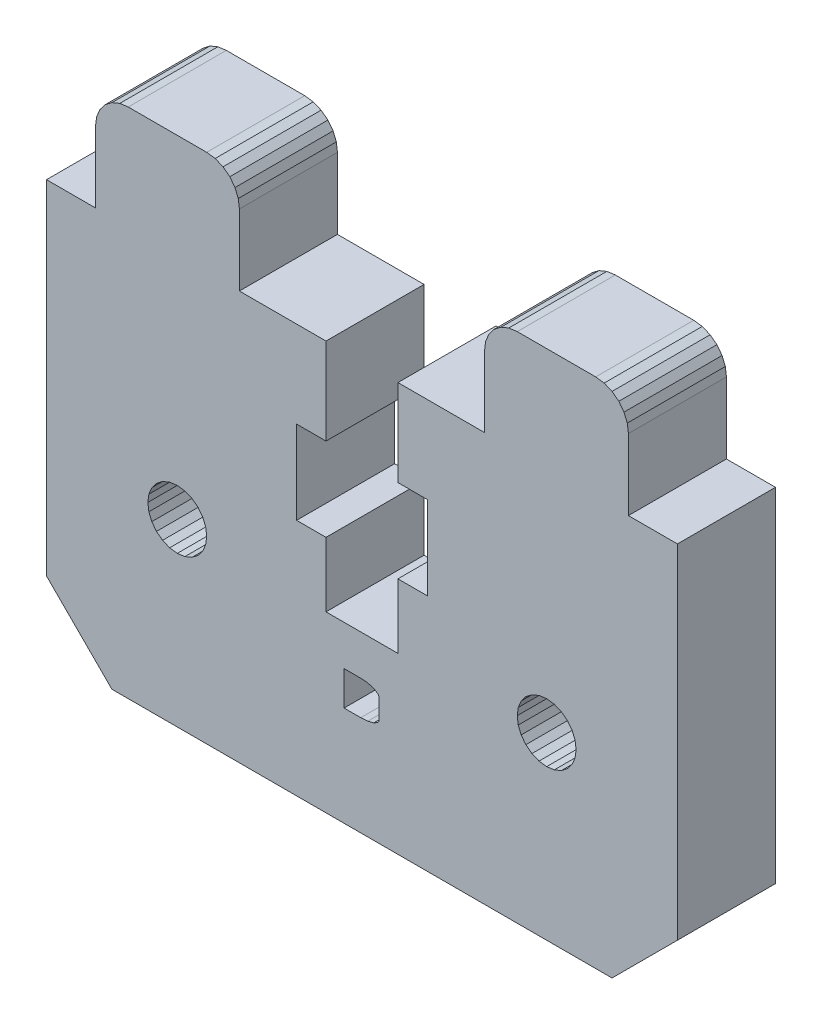
SolidWorks part; units mm, degrees
material "Maple"
ref_plane "Front Plane" through (0, 0, 0) normal (0, 0, 1) x (1, 0, 0)
ref_plane "Top Plane" through (0, 0, 0) normal (0, 1, 0) x (1, 0, 0)
ref_plane "Right Plane" through (0, 0, 0) normal (1, 0, 0) x (0, 0, -1)
sketch "Sketch1" plane through (0, 0, 0) normal (0, 0, 1) x (1, 0, 0)
  line L7236 (361.8223, 316.3766) -> (362.2365, 316.6945)
  line L7237 (368.5541, 316.8943) -> (368.0365, 316.9624)
  line L7238 (363.2365, 296.6124) -> (363.2978, 296.1466)
  line L7239 (341.1637, 297.8852) -> (340.8776, 297.5124)
  line L7240 (337.5046, 315.4801) -> (337.7044, 315.9624)
  line L7241 (346.2365, 314.9624) -> (346.1683, 315.4801)
  line L7242 (344.1751, 297.0783) -> (343.9953, 297.5124)
  line L7243 (366.7751, 297.0783) -> (366.5953, 297.5124)
  line L7244 (364.1365, 298.1713) -> (363.7637, 297.8852)
  line L7245 (345.6507, 316.3766) -> (345.2365, 316.6945)
  line L7246 (338.4365, 285.6124) -> (369.0365, 285.6124)
  line L7247 (369.0365, 285.6124) -> (373.0365, 289.6124)
  line L7248 (373.0365, 310.6124) -> (373.0365, 289.6124)
  line L7249 (370.0365, 310.6124) -> (373.0365, 310.6124)
  line L7250 (370.0365, 314.9624) -> (370.0365, 310.6124)
  line L7251 (370.0365, 314.9624) -> (369.9683, 315.4801)
  line L7252 (369.9683, 315.4801) -> (369.7685, 315.9624)
  line L7253 (369.7685, 315.9624) -> (369.4507, 316.3766)
  line L7254 (369.4507, 316.3766) -> (369.0365, 316.6945)
  line L7255 (369.0365, 316.6945) -> (368.5541, 316.8943)
  line L7256 (363.2365, 316.9624) -> (368.0365, 316.9624)
  line L7257 (362.7188, 316.8943) -> (363.2365, 316.9624)
  line L7258 (362.2365, 316.6945) -> (362.7188, 316.8943)
  line L7259 (361.5044, 315.9624) -> (361.8223, 316.3766)
  line L7260 (361.3046, 315.4801) -> (361.5044, 315.9624)
  line L7261 (361.2365, 314.9624) -> (361.3046, 315.4801)
  line L7262 (361.2365, 310.6124) -> (361.2365, 314.9624)
  line L7263 (355.9365, 310.6124) -> (361.2365, 310.6124)
  line L7264 (355.9365, 305.3124) -> (355.9365, 310.6124)
  line L7265 (357.7365, 305.3124) -> (355.9365, 305.3124)
  line L7266 (357.7365, 300.2124) -> (357.7365, 305.3124)
  line L7267 (355.9365, 300.2124) -> (357.7365, 300.2124)
  line L7268 (355.9365, 296.2624) -> (355.9365, 300.2124)
  line L7269 (351.5365, 296.2624) -> (355.9365, 296.2624)
  line L7270 (351.5365, 300.2124) -> (351.5365, 296.2624)
  line L7271 (349.7365, 300.2124) -> (351.5365, 300.2124)
  line L7272 (349.7365, 305.3124) -> (349.7365, 300.2124)
  line L7273 (351.5365, 305.3124) -> (349.7365, 305.3124)
  line L7274 (351.5365, 310.6124) -> (351.5365, 305.3124)
  line L7275 (346.2365, 310.6124) -> (351.5365, 310.6124)
  line L7276 (346.2365, 314.9624) -> (346.2365, 310.6124)
  line L7277 (346.1683, 315.4801) -> (345.9685, 315.9624)
  line L7278 (345.9685, 315.9624) -> (345.6507, 316.3766)
  line L7279 (345.2365, 316.6945) -> (344.7541, 316.8943)
  line L7280 (344.7541, 316.8943) -> (344.2365, 316.9624)
  line L7281 (339.4365, 316.9624) -> (344.2365, 316.9624)
  line L7282 (338.9188, 316.8943) -> (339.4365, 316.9624)
  line L7283 (338.4365, 316.6945) -> (338.9188, 316.8943)
  line L7284 (338.0223, 316.3766) -> (338.4365, 316.6945)
  line L7285 (337.7044, 315.9624) -> (338.0223, 316.3766)
  line L7286 (337.4365, 314.9624) -> (337.5046, 315.4801)
  line L7287 (337.4365, 310.6124) -> (337.4365, 314.9624)
  line L7288 (337.4365, 310.6124) -> (334.4365, 310.6124)
  line L7289 (334.4365, 310.6124) -> (334.4365, 289.6124)
  line L7290 (338.4365, 285.6124) -> (334.4365, 289.6124)
  line L7291 (363.4776, 295.7124) -> (363.7637, 295.3396)
  line L7292 (363.2978, 296.1466) -> (363.4776, 295.7124)
  line L7293 (363.2978, 297.0783) -> (363.2365, 296.6124)
  line L7294 (363.4776, 297.5124) -> (363.2978, 297.0783)
  line L7295 (363.7637, 297.8852) -> (363.4776, 297.5124)
  line L7296 (364.5706, 298.3511) -> (364.1365, 298.1713)
  line L7297 (365.0365, 298.4124) -> (364.5706, 298.3511)
  line L7298 (365.5023, 298.3511) -> (365.0365, 298.4124)
  line L7299 (365.9365, 298.1713) -> (365.5023, 298.3511)
  line L7300 (366.3093, 297.8852) -> (365.9365, 298.1713)
  line L7301 (366.5953, 297.5124) -> (366.3093, 297.8852)
  line L7302 (366.8365, 296.6124) -> (366.7751, 297.0783)
  line L7303 (366.7751, 296.1466) -> (366.8365, 296.6124)
  line L7304 (366.5953, 295.7124) -> (366.7751, 296.1466)
  line L7305 (366.3093, 295.3396) -> (366.5953, 295.7124)
  line L7306 (365.9365, 295.0536) -> (366.3093, 295.3396)
  line L7307 (365.5023, 294.8738) -> (365.9365, 295.0536)
  line L7308 (365.0365, 294.8124) -> (365.5023, 294.8738)
  line L7309 (364.5706, 294.8738) -> (365.0365, 294.8124)
  line L7310 (364.1365, 295.0536) -> (364.5706, 294.8738)
  line L7311 (363.7637, 295.3396) -> (364.1365, 295.0536)
  line L7312 (341.9706, 298.3511) -> (341.5365, 298.1713)
  line L7313 (342.4365, 298.4124) -> (341.9706, 298.3511)
  line L7314 (342.9023, 298.3511) -> (342.4365, 298.4124)
  line L7315 (343.3365, 298.1713) -> (342.9023, 298.3511)
  line L7316 (343.7093, 297.8852) -> (343.3365, 298.1713)
  line L7317 (343.9953, 297.5124) -> (343.7093, 297.8852)
  line L7318 (344.2365, 296.6124) -> (344.1751, 297.0783)
  line L7319 (344.1751, 296.1466) -> (344.2365, 296.6124)
  line L7320 (343.9953, 295.7124) -> (344.1751, 296.1466)
  line L7321 (343.7093, 295.3396) -> (343.9953, 295.7124)
  line L7322 (343.3365, 295.0536) -> (343.7093, 295.3396)
  line L7323 (342.9023, 294.8738) -> (343.3365, 295.0536)
  line L7324 (342.4365, 294.8124) -> (342.9023, 294.8738)
  line L7325 (341.9706, 294.8738) -> (342.4365, 294.8124)
  line L7326 (341.5365, 295.0536) -> (341.9706, 294.8738)
  line L7327 (341.1637, 295.3396) -> (341.5365, 295.0536)
  line L7328 (340.8776, 295.7124) -> (341.1637, 295.3396)
  line L7329 (340.6978, 296.1466) -> (340.8776, 295.7124)
  line L7330 (340.6365, 296.6124) -> (340.6978, 296.1466)
  line L7331 (340.6978, 297.0783) -> (340.6365, 296.6124)
  line L7332 (340.8776, 297.5124) -> (340.6978, 297.0783)
  line L7333 (341.5365, 298.1713) -> (341.1637, 297.8852)
  line L9610 (353.66, 291.718) -> (354.0932, 291.7484)
  line L9611 (354.0932, 291.7484) -> (354.4561, 291.8397)
  line L9612 (354.4561, 291.8397) -> (354.7019, 291.981)
  line L9613 (354.7019, 291.981) -> (354.7634, 292.0662)
  line L9614 (354.7634, 292.0662) -> (354.7839, 292.1613)
  line L9615 (354.7839, 292.1613) -> (354.7839, 293.3289)
  line L9616 (354.7839, 293.3289) -> (354.7634, 293.425)
  line L9617 (354.7634, 293.425) -> (354.7019, 293.5138)
  line L9618 (354.7019, 293.5138) -> (354.4561, 293.6691)
  line L9619 (354.4561, 293.6691) -> (354.0932, 293.7745)
  line L9620 (354.0932, 293.7745) -> (353.66, 293.8097)
  line L9621 (353.66, 293.8097) -> (352.6422, 293.8097)
  line L9622 (352.6422, 293.8097) -> (352.6422, 291.718)
  line L9623 (352.6422, 291.718) -> (353.66, 291.718)
  line L9624 (352.6422, 289.5017) -> (352.6422, 293.8097)
  line L9625 (352.6422, 293.8097) -> (353.66, 293.8097)
  line L9626 (353.66, 293.8097) -> (354.0932, 293.7745)
  line L9627 (354.0932, 293.7745) -> (354.4561, 293.6692)
  line L9628 (354.4561, 293.6692) -> (354.7019, 293.5139)
  line L9629 (354.7019, 293.5139) -> (354.7634, 293.4251)
  line L9630 (354.7634, 293.4251) -> (354.7839, 293.3289)
  line L9631 (354.7839, 293.3289) -> (354.7839, 292.1614)
  line L9632 (354.7839, 292.1614) -> (354.7634, 292.0664)
  line L9633 (354.7634, 292.0664) -> (354.7019, 291.9811)
  line L9634 (354.7019, 291.9811) -> (354.4561, 291.8399)
  line L9635 (354.4561, 291.8399) -> (354.0932, 291.7486)
  line L9636 (354.0932, 291.7486) -> (353.66, 291.7181)
  line L9637 (353.66, 291.7181) -> (352.6422, 291.7181)
  line L9638 (352.6422, 291.7181) -> (352.6422, 289.5017)
extrude "Boss-Extrude1" add sketch "Sketch1" along normal blind 6 contours L7290 L7246 L7247 L7248 L7249 L7250 L7251 L7252 L7253 L7254 L7255 L7237 L7256 L7257 L7258 L7236 L7259 L7260 L7261 L7262 L7263 L7264 L7265 L7266 L7267 L7268 L7269 L7270 L7271 L7272 L7273 L7274 L7275 L7276 L7241 L7277 L7278 L7245 L7279 L7280 L7281 L7282 L7283 L7284 L7285 L7240 L7286 L7287 L7288 L7289
